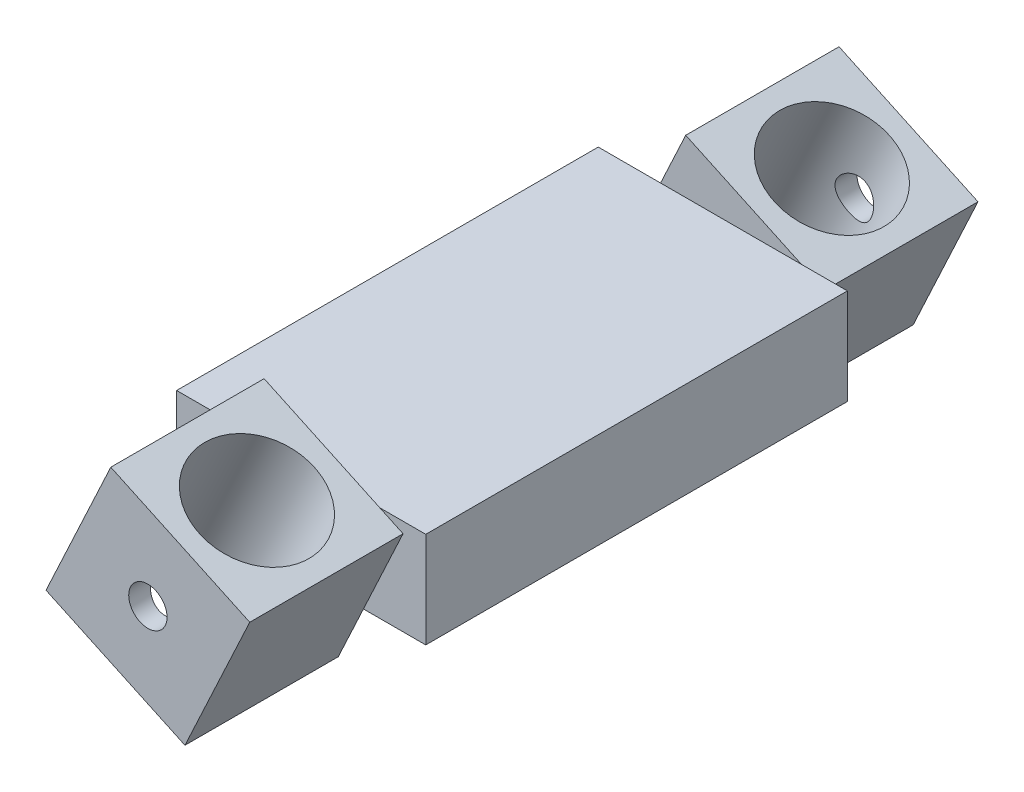
SolidWorks part; units mm, degrees
ref_plane "Front Plane" through (0, 0, 0) normal (0, 0, 1) x (1, 0, 0)
ref_plane "Top Plane" through (0, 0, 0) normal (0, 1, 0) x (1, 0, 0)
ref_plane "Right Plane" through (0, 0, 0) normal (1, 0, 0) x (0, 0, -1)
sketch "Sketch1" plane through (0, 0, 0) normal (0, 0, 1) x (1, 0, 0)
  line L0 (0, 0) -> (-7.2505, 3.3809)
  line L1 (-7.2505, 3.3809) -> (-3.8695, 10.6314)
  line L2 (-3.8695, 10.6314) -> (3.3809, 7.2505)
  line L3 (3.3809, 7.2505) -> (0, 0)
  line L4 (0, 0) -> (6.7577, 0) construction
  dimension "D1" = 65
  dimension "D2" = 8
extrude "Boss-Extrude1" add sketch "Sketch1" along normal blind 8
sketch "Sketch2" plane through (0, 0, 8) normal (0, 0, 1) x (1, 0, 0)
  line L6 (-6.0383, 2.8157) -> (1.313, 2.8157)
  line L7 (-7.2505, 3.3809) -> (0, 0) construction
  line L8 (0, 0) -> (3.3809, 7.2505) construction
  line L9 (1.313, 2.8157) -> (3.3809, 7.2505)
  line L10 (3.3809, 7.2505) -> (2.1688, 7.8157)
  line L11 (3.3809, 7.2505) -> (-3.8695, 10.6314) construction
  line L12 (2.1688, 7.8157) -> (-5.1825, 7.8157)
  line L13 (-3.8695, 10.6314) -> (-7.2505, 3.3809) construction
  line L14 (-5.1825, 7.8157) -> (-7.2505, 3.3809)
  line L15 (-7.2505, 3.3809) -> (-6.0383, 2.8157)
  dimension "D1" = 5
extrude "Boss-Extrude2" add sketch "Sketch2" along normal blind 11
sketch "Sketch3" plane through (0, 0, 8) normal (0, 0, 1) x (1, 0, 0)
  line L0 (-5.1825, 7.8157) -> (-8.4348, 7.8157)
  line L1 (1.313, 2.8157) -> (4.5652, 2.8157)
  line L2 (4.5652, 2.8157) -> (4.5652, 7.8157)
  line L3 (4.5652, 7.8157) -> (2.1688, 7.8157)
  line L4 (2.1688, 7.8157) -> (3.3809, 7.2505)
  line L5 (3.3809, 7.2505) -> (1.313, 2.8157)
  line L6 (-6.0383, 2.8157) -> (-8.4348, 2.8157)
  line L7 (-8.4348, 2.8157) -> (-8.4348, 7.8157)
  line L8 (-6.0383, 2.8157) -> (-7.2505, 3.3809)
  line L9 (-7.2505, 3.3809) -> (-5.1825, 7.8157)
  point P14 (3.581, 7.8157)
  dimension "D1" = 13
extrude "Boss-Extrude3" add sketch "Sketch3" along normal up to surface (11 mm away) up to face at (-1.9348, 5.3157, 19)
sketch "Sketch5" plane through (0, 0, 0) normal (0, 0, -1) x (-1, 0, 0)
  line L0 (0, 0) -> (-3.3809, 7.2505) construction
  line L1 (-3.3809, 7.2505) -> (3.8695, 10.6314) construction
  circle A0 centre (1.9348, 5.3157) radius 1
  dimension "D1" = 4
  dimension "D2" = 4
  dimension "D3" = 2
extrude "Cut-Extrude2" cut sketch "Sketch5" against normal blind 4
mirror "Mirror2" of bodies 107 102
sketch "Sketch4" plane through (3.3809, 7.2505, 0) normal (0.4226, 0.9063, 0) x (0.9063, -0.4226, 0)
  line L0 (0, 0) -> (-8, 0) construction
  line L1 (-8, -8) -> (-8, 0) construction
  line L2 (0, -38) -> (-8, -38) construction
  circle A0 centre (-4, -4) radius 3
  circle A1 centre (-4, -34) radius 3
  point P4 (0, 0)
  dimension "D1" = 6
  dimension "D2" = 4
  dimension "D3" = 4
  dimension "D4" = 4
extrude "Cut-Extrude1" cut sketch "Sketch4" against normal up to next
